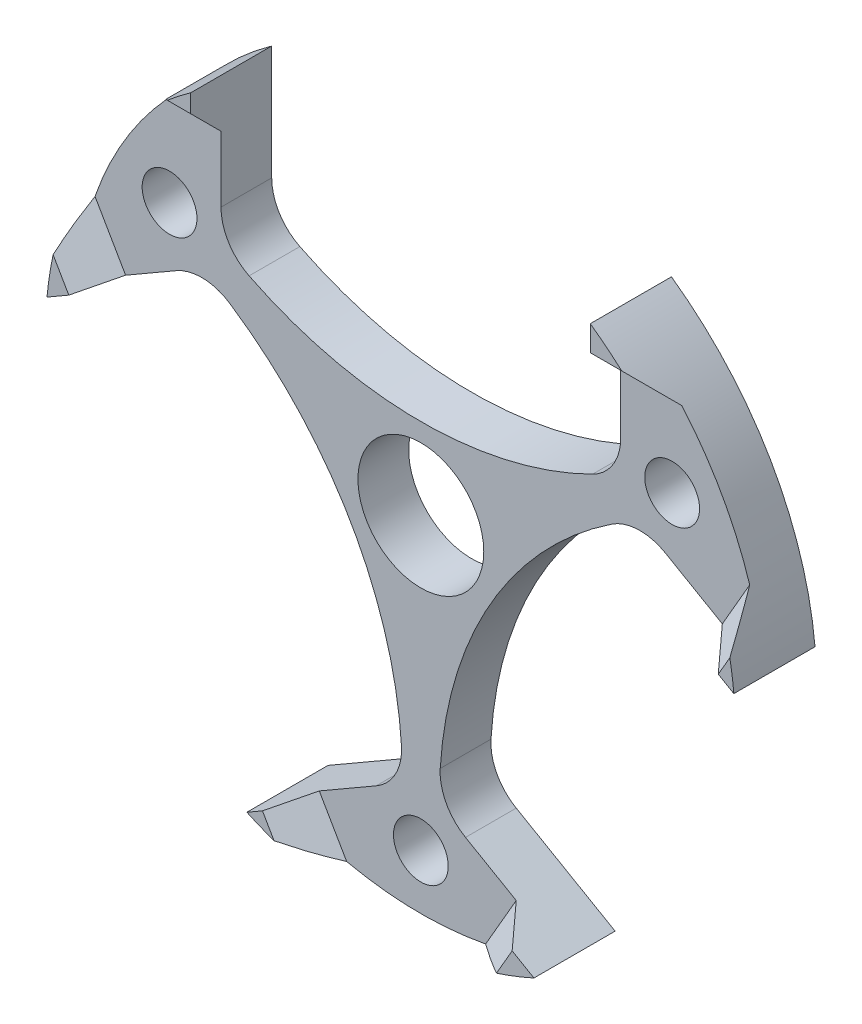
SolidWorks part; units mm, degrees
material "7075-T6 (SN)"
ref_plane "Face" through (0, 0, 0) normal (0, 0, 1) x (1, 0, 0)
ref_plane "Dessus" through (0, 0, 0) normal (0, 1, 0) x (1, 0, 0)
ref_plane "Droite" through (0, 0, 0) normal (1, 0, 0) x (0, 0, -1)
sketch "Esquisse1" plane through (0, 0, 0) normal (0, 0, 1) x (1, 0, 0)
  circle A0 centre (0, 0) radius 17
  dimension "D1" = 34
extrude "Boss.-Extru.1" add sketch "Esquisse1" along normal mid plane 2.5
sketch "Esquisse2" plane through (0, 0, 1.25) normal (0, 0, 1) x (1, 0, 0)
  line L0 (-9.85, 13.8556) -> (-9.85, 8.2275)
  line L1 (9.85, 8.2275) -> (9.85, 13.8556)
  circle A0 centre (0, 0) radius 17 construction
  arc A1 (9.85, 13.8556) -> (-9.85, 13.8556) centre (0, 0) ccw
  arc A2 (-8.4636, 5.9892) -> (8.4636, 5.9892) centre (0, 23) ccw
  arc A3 (8.4636, 5.9892) -> (9.85, 8.2275) centre (7.35, 8.2275) ccw
  arc A4 (-9.85, 8.2275) -> (-8.4636, 5.9892) centre (-7.35, 8.2275) ccw
  dimension "D2" = 19
  dimension "D4" = 2.5
  dimension "D1" = 19.7
  dimension "D3" = 23
extrude "Enlèv. mat.-Extru.1" cut sketch "Esquisse2" against normal through all
hole_wizard "Dégagement M2.51" positions "Esquisse4" profile "Esquisse3" hole size "M2.5" standard "DIN" end condition through all
sketch "Esquisse4" plane through (0, 0, 1.25) normal (0, 0, 1) x (1, 0, 0)
  line L0 (0, 0) -> (12.3842, 7.15) construction
  line L2 (0, 0) -> (0, 10.3256) construction
  point P0 (12.3842, 7.15)
  dimension "D1" = 60
  dimension "D2" = 14.3
sketch "Esquisse3" plane through (12.3842, 7.15, 1.25) normal (1, 0, 0) x (0, -1, 0)
  line L0 (0, 0) -> (0, 2.5)
  line L1 (0, 2.5) -> (1.35, 2.5)
  line L2 (1.35, 2.5) -> (1.35, 0)
  line L5 (1.35, 0) -> (0, 0)
  line L11 (0, -6.35) -> (0, 107.95) construction
  dimension "Diamètre du perçage jusqu'au prochain" = 2.7
  dimension "Profondeur du perçage jusqu'au prochain" = 2.5
pattern_circular "Répétition circulaire1" count 3 over 360 about axis through (0, 0, 0) along (0, 0, 1) of "Enlèv. mat.-Extru.1", "Dégagement M2.51"
hole_wizard "Diamètre du perçage Ø6.2 (6.2)1" positions "Esquisse6" profile "Esquisse5" hole size "Ø6.2" standard "DIN" end condition through all
sketch "Esquisse6" plane through (0, 0, 1.25) normal (0, 0, 1) x (1, 0, 0)
  point P0 (0, 0)
sketch "Esquisse5" plane through (0, 0, 1.25) normal (1, 0, 0) x (0, -1, 0)
  line L0 (0, 0) -> (0, 2.5)
  line L1 (0, 2.5) -> (3.1, 2.5)
  line L2 (3.1, 2.5) -> (3.1, 0)
  line L5 (3.1, 0) -> (0, 0)
  line L11 (0, -6.35) -> (0, 107.95) construction
  dimension "Diamètre du perçage jusqu'au prochain" = 6.2
  dimension "Profondeur du perçage jusqu'au prochain" = 2.5
sketch "Esquisse8" plane through (-9.85, 0, 0) normal (1, 0, 0) x (0, 0, -1)
  line L0 (-1.25, 11.4678) -> (-2.75, 12.9678)
  line L1 (-1.25, 13.8556) -> (-1.25, 8.2275) construction
  line L2 (-2.75, 12.9678) -> (-2.75, 13.8556)
  line L3 (-2.75, 13.8556) -> (-1.25, 13.8556)
  line L4 (-1.25, 13.8556) -> (-1.25, 11.4678)
  line L5 (1.25, 13.8556) -> (1.25, 8.2275) construction
  line L7 (1.25, 1.6026) -> (1.25, 13.8556) construction
  circle A0 centre (-3.05, 11.5) radius 1.25 construction
  dimension "D3" = 2.5
  dimension "D5" = 4.3
  dimension "D1" = 45
  dimension "D2" = 4
  dimension "D4" = 11.5
extrude "Boss.-Extru.2" add sketch "Esquisse8" against normal up to surface up to face at (-14.0548, 8.1145, 0)
sketch "Esquisse9" plane through (9.85, 0, 0) normal (-1, 0, 0) x (0, 0, 1)
  line L0 (1.25, 13.8556) -> (2.75, 13.8556)
  line L1 (2.75, 13.8556) -> (2.75, 12.6142)
  line L2 (2.75, 12.6142) -> (1.25, 11.1142)
  line L3 (1.25, 8.2275) -> (1.25, 13.8556) construction
  line L4 (1.25, 11.1142) -> (1.25, 13.8556)
  line L5 (2.75, 12.9678) -> (2.75, 13.8556) construction
  line L6 (1.25, 11.4678) -> (2.75, 12.9678) construction
  circle A0 centre (3.05, 11.5) radius 1 construction
  dimension "D1" = 2
extrude "Boss.-Extru.3" add sketch "Esquisse9" against normal up to surface (3.0137 mm away)
pattern_circular "Répétition circulaire2" count 3 over 360 about axis through (0, 0, 0) along (0, 0, 1) of "Boss.-Extru.2", "Boss.-Extru.3"
